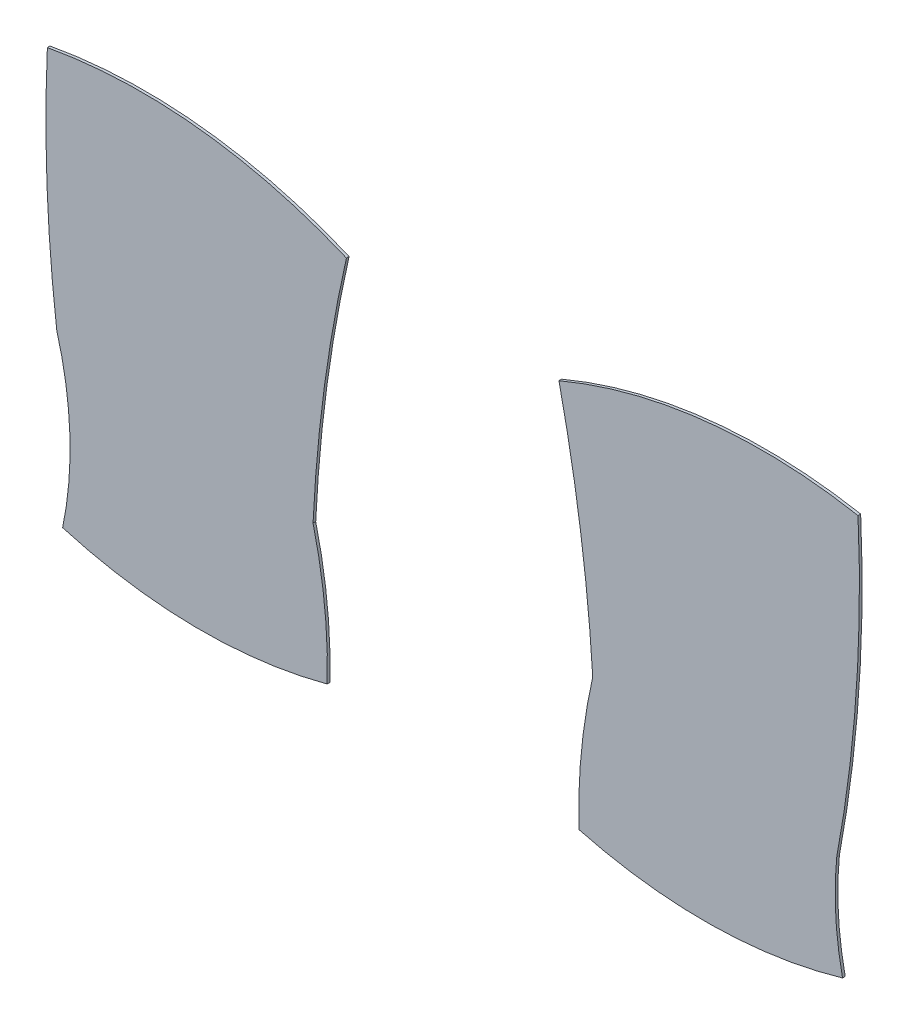
SolidWorks part; units mm, degrees
ref_plane "Alzado" through (0, 0, 0) normal (0, 0, 1) x (1, 0, 0)
ref_plane "Planta" through (0, 0, 0) normal (0, 1, 0) x (1, 0, 0)
ref_plane "Vista lateral" through (0, 0, 0) normal (1, 0, 0) x (0, 0, -1)
sketch "Model" plane through (0, 0, 0) normal (0, 0, 1) x (1, 0, 0)
  arc A0 (38.7276, 40.831) -> (39.0826, 31.775) centre (92.8226, 38.4165) ccw
  arc A1 (39.3039, 25.4513) -> (39.0826, 31.775) centre (26.3398, 28.1635) ccw
  arc A2 (39.3039, 25.4513) -> (49.2719, 25.3337) centre (44.498, 43.2072) ccw
  arc A3 (49.2719, 25.3337) -> (48.7388, 30.3173) centre (30.7585, 25.8736) ccw
  arc A4 (49.9964, 39.5978) -> (48.7388, 30.3173) centre (102.1468, 27.8054) ccw
  arc A5 (49.9964, 39.5978) -> (38.7276, 40.831) centre (42.3039, 21.4062) ccw
  arc A6 (59.2773, 30.5656) -> (58.0039, 39.5984) centre (1.0789, 26.9675) ccw
  arc A7 (59.2773, 30.5656) -> (58.7504, 25.3274) centre (80.1714, 25.8183) ccw
  arc A8 (58.7504, 25.3274) -> (68.6906, 25.4501) centre (63.5005, 43.2072) ccw
  arc A9 (68.4699, 29.287) -> (68.6906, 25.4501) centre (80.8682, 28.0752) ccw
  arc A10 (68.4699, 29.287) -> (69.2725, 40.8332) centre (19.2591, 38.5085) ccw
  arc A11 (69.2725, 40.8332) -> (58.0039, 39.5984) centre (65.6991, 21.4079) ccw
extrude "Saliente-Extruir1" add sketch "Model" along normal blind 0.1
